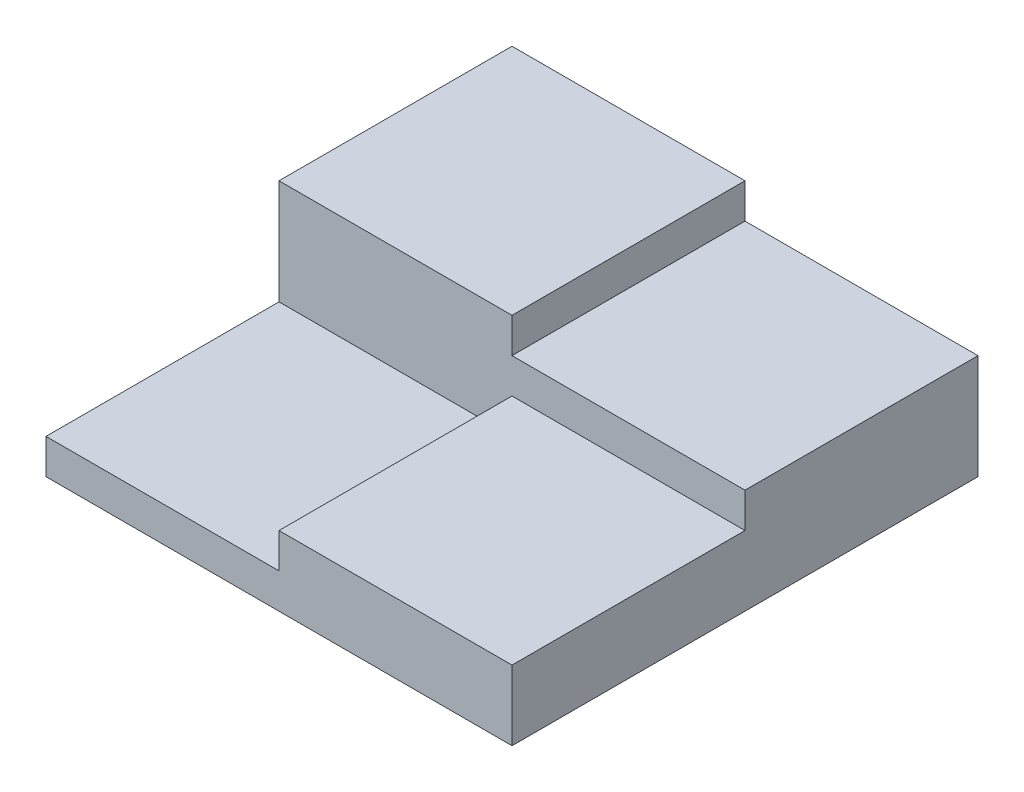
SolidWorks part; units mm, degrees
ref_plane "Front Plane" through (0, 0, 0) normal (0, 0, 1) x (1, 0, 0)
ref_plane "Top Plane" through (0, 0, 0) normal (0, 1, 0) x (1, 0, 0)
ref_plane "Right Plane" through (0, 0, 0) normal (1, 0, 0) x (0, 0, -1)
sketch "Sketch1" plane through (0, 0, 0) normal (0, 1, 0) x (1, 0, 0)
  line L1 (-10, -10) -> (10, -10)
  line L2 (-10, -10) -> (-10, 10)
  line L3 (-10, 10) -> (10, 10)
  line L4 (10, -10) -> (10, 10)
  line L5 (-10, -10) -> (10, 10) construction
  line L6 (-10, 10) -> (10, -10) construction
  point P0 (0, 0)
  dimension "D1" = 20
  dimension "D2" = 20
extrude "Extrude1" add sketch "Sketch1" along normal blind 1.5
sketch "Sketch2" plane through (0, 1.5, 0) normal (0, 1, 0) x (1, 0, 0)
  line L0 (-10, 10) -> (-10, -10) construction
  line L1 (-10, 0) -> (10, 0)
  line L2 (-10, 0) -> (-10, 10)
  line L3 (-10, 10) -> (10, 10)
  line L4 (10, 0) -> (10, 10)
extrude "Extrude2" add sketch "Sketch2" along normal blind 3
sketch "Sketch3" plane through (0, 1.5, 0) normal (0, 1, 0) x (1, 0, 0)
  line L0 (-10, 0) -> (10, 0) construction
  line L1 (0, 0) -> (10, 0)
  line L2 (0, 0) -> (0, -10)
  line L3 (0, -10) -> (10, -10)
  line L4 (10, 0) -> (10, -10)
extrude "Extrude3" add sketch "Sketch3" along normal blind 1.5
sketch "Sketch4" plane through (0, 4.5, 0) normal (0, 1, 0) x (-1, 0, 0)
  line L2 (0, 0) -> (10, 0)
  line L3 (0, 0) -> (0, -10)
  line L4 (0, -10) -> (10, -10)
  line L5 (10, 0) -> (10, -10)
extrude "Extrude4" add sketch "Sketch4" along normal blind 1.5
sketch "Sketch6" plane through (0, 3, 0) normal (0, 1, 0) x (1, 0, 0)
  line L0 (10, -5) -> (0, -5)
  line L1 (10, -10) -> (10, 0) construction
  line L2 (0, 0) -> (0, -10) construction
  line L3 (5, 0) -> (5, -10)
  line L4 (10, 0) -> (0, 0) construction
  line L5 (0, -10) -> (10, -10) construction
sketch "Sketch8" plane through (0, 1.5, 0) normal (0, 1, 0) x (1, 0, 0)
  line L0 (-5, 0) -> (-5, -10)
  line L1 (-10, 0) -> (0, 0) construction
  line L2 (-10, -10) -> (0, -10) construction
  line L3 (-10, -5) -> (0, -5)
  line L4 (-10, 0) -> (-10, -10) construction
  line L5 (0, 0) -> (0, -10) construction
sketch "Sketch10" plane through (0, 4.5, 0) normal (0, 1, 0) x (-1, 0, 0)
  line L0 (-5, -10) -> (-5, 0)
  line L1 (-10, -10) -> (0, -10) construction
  line L2 (0, 0) -> (-10, 0) construction
  line L3 (0, -5) -> (-10, -5)
  line L4 (0, 0) -> (0, -10) construction
  line L5 (-10, 0) -> (-10, -10) construction
sketch "Sketch11" plane through (0, 6, 0) normal (0, 1, 0) x (-1, 0, 0)
  line L0 (5, -10) -> (5, 0)
  line L1 (0, -10) -> (10, -10) construction
  line L2 (10, 0) -> (0, 0) construction
  line L3 (10, -5) -> (0, -5)
  line L4 (10, -10) -> (10, 0) construction
  line L5 (0, 0) -> (0, -10) construction
